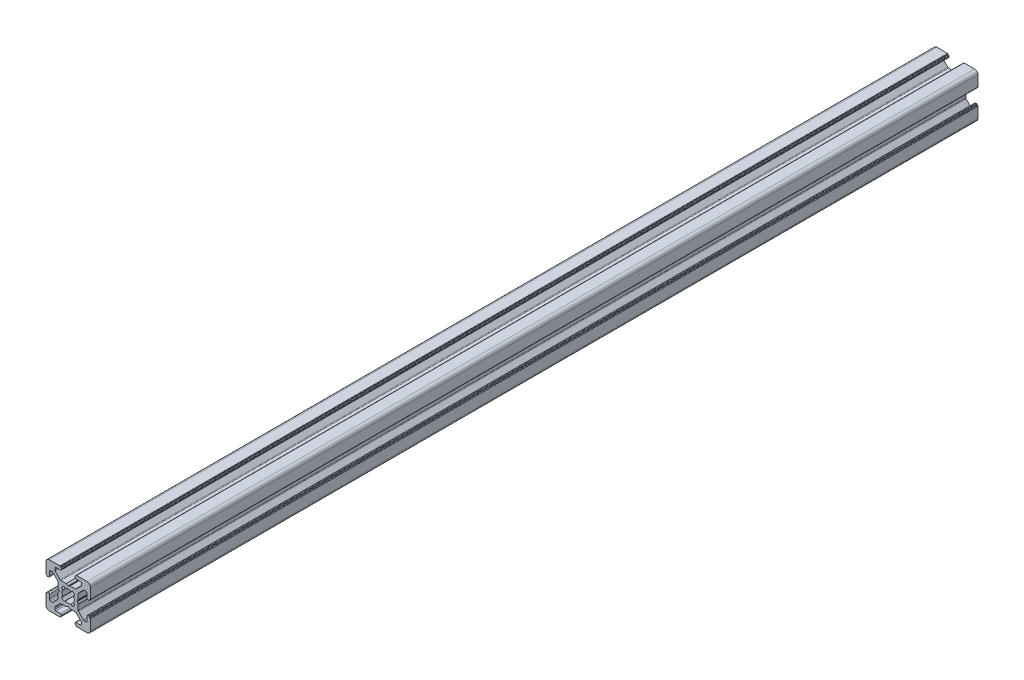
SolidWorks part; units mm, degrees
ref_plane "Płaszczyzna przednia" through (0, 0, 0) normal (0, 0, 1) x (1, 0, 0)
ref_plane "Płaszczyzna górna" through (0, 0, 0) normal (0, 1, 0) x (1, 0, 0)
ref_plane "Płaszczyzna prawa" through (0, 0, 0) normal (1, 0, 0) x (0, 0, -1)
sketch "Szkic1" plane through (0, 0, 0) normal (0, 0, 1) x (1, 0, 0)
  line L0 (7.0078, -1.8401) -> (7.5547, -2.4918)
  line L1 (7.5547, -5.0082) -> (7.0078, -5.6599)
  line L2 (8.0861, -6.7396) -> (8.7418, -6.1953)
  line L3 (11.2582, -6.1953) -> (11.9139, -6.7396)
  line L4 (12.9922, -5.6599) -> (12.4453, -5.0082)
  line L5 (12.4453, -2.4918) -> (12.9922, -1.8401)
  line L6 (11.9139, -0.7604) -> (11.2582, -1.3047)
  line L7 (8.7418, -1.3047) -> (8.0861, -0.7604)
  line L8 (6.25, 6.25) -> (1.5, 6.25)
  line L9 (6.45, 5.95) -> (6.45, 6.05)
  line L10 (6.8, 5.75) -> (6.65, 5.75)
  line L11 (7, 5.25) -> (7, 5.55)
  line L12 (4.5, 4.75) -> (6.5, 4.75)
  line L13 (4, 3.5178) -> (4, 4.25)
  line L14 (6.4142, 0.8964) -> (4.1464, 3.1642)
  line L15 (9.0464, 0.75) -> (6.7678, 0.75)
  line L16 (9.9, 0.2881) -> (9.1464, 0.7232)
  line L17 (10.8536, 0.7232) -> (10.1, 0.2881)
  line L18 (13.2322, 0.75) -> (10.9536, 0.75)
  line L19 (15.8536, 3.1642) -> (13.5858, 0.8964)
  line L20 (16, 4.25) -> (16, 3.5178)
  line L21 (13.5, 4.75) -> (15.5, 4.75)
  line L22 (13, 5.55) -> (13, 5.25)
  line L23 (13.35, 5.75) -> (13.2, 5.75)
  line L24 (13.55, 6.05) -> (13.55, 5.95)
  line L25 (18.5, 6.25) -> (13.75, 6.25)
  line L26 (20, 0) -> (20, 4.75)
  line L27 (19.7, -0.2) -> (19.8, -0.2)
  line L28 (19.5, -0.55) -> (19.5, -0.4)
  line L29 (19, -0.75) -> (19.3, -0.75)
  line L30 (18.5, 1.75) -> (18.5, -0.25)
  line L31 (17.2678, 2.25) -> (18, 2.25)
  line L32 (14.6464, -0.1642) -> (16.9142, 2.1036)
  line L33 (14.5, -2.7964) -> (14.5, -0.5178)
  line L34 (14.0381, -3.65) -> (14.4732, -2.8964)
  line L35 (14.4732, -4.6036) -> (14.0381, -3.85)
  line L36 (14.5, -6.9822) -> (14.5, -4.7036)
  line L37 (16.9142, -9.6036) -> (14.6464, -7.3358)
  line L38 (18, -9.75) -> (17.2678, -9.75)
  line L39 (18.5, -7.25) -> (18.5, -9.25)
  line L40 (19.3, -6.75) -> (19, -6.75)
  line L41 (19.5, -7.1) -> (19.5, -6.95)
  line L42 (19.8, -7.3) -> (19.7, -7.3)
  line L43 (20, -12.25) -> (20, -7.5)
  line L44 (13.75, -13.75) -> (18.5, -13.75)
  line L45 (13.55, -13.45) -> (13.55, -13.55)
  line L46 (13.2, -13.25) -> (13.35, -13.25)
  line L47 (13, -12.75) -> (13, -13.05)
  line L48 (15.5, -12.25) -> (13.5, -12.25)
  line L49 (16, -11.0178) -> (16, -11.75)
  line L50 (13.5858, -8.3964) -> (15.8536, -10.6642)
  line L51 (10.9536, -8.25) -> (13.2322, -8.25)
  line L52 (10.1, -7.7881) -> (10.8536, -8.2232)
  line L53 (9.1464, -8.2232) -> (9.9, -7.7881)
  line L54 (6.7678, -8.25) -> (9.0464, -8.25)
  line L55 (4.1464, -10.6642) -> (6.4142, -8.3964)
  line L56 (4, -11.75) -> (4, -11.0178)
  line L57 (6.5, -12.25) -> (4.5, -12.25)
  line L58 (7, -13.05) -> (7, -12.75)
  line L59 (6.65, -13.25) -> (6.8, -13.25)
  line L60 (6.45, -13.55) -> (6.45, -13.45)
  line L61 (1.5, -13.75) -> (6.25, -13.75)
  line L62 (0, -7.5) -> (0, -12.25)
  line L63 (0.3, -7.3) -> (0.2, -7.3)
  line L64 (0.5, -6.95) -> (0.5, -7.1)
  line L65 (1, -6.75) -> (0.7, -6.75)
  line L66 (1.5, -9.25) -> (1.5, -7.25)
  line L67 (2.7322, -9.75) -> (2, -9.75)
  line L68 (5.3536, -7.3358) -> (3.0858, -9.6036)
  line L69 (5.5, -4.7036) -> (5.5, -6.9822)
  line L70 (5.9619, -3.85) -> (5.5268, -4.6036)
  line L71 (5.5268, -2.8964) -> (5.9619, -3.65)
  line L72 (5.5, -0.5178) -> (5.5, -2.7964)
  line L73 (3.0858, 2.1036) -> (5.3536, -0.1642)
  line L74 (2, 2.25) -> (2.7322, 2.25)
  line L75 (1.5, -0.25) -> (1.5, 1.75)
  line L76 (0.7, -0.75) -> (1, -0.75)
  line L77 (0.5, -0.4) -> (0.5, -0.55)
  line L78 (0.2, -0.2) -> (0.3, -0.2)
  line L79 (0, 4.75) -> (0, 0)
  arc A0 (7.5547, -2.4918) -> (7.5547, -5.0082) centre (10, -3.75) ccw
  arc A1 (7.0078, -5.6599) -> (8.0861, -6.7396) centre (10, -3.75) ccw
  arc A2 (8.7418, -6.1953) -> (11.2582, -6.1953) centre (10, -3.75) ccw
  arc A3 (11.9139, -6.7396) -> (12.9922, -5.6599) centre (10, -3.75) ccw
  arc A4 (12.4453, -5.0082) -> (12.4453, -2.4918) centre (10, -3.75) ccw
  arc A5 (12.9922, -1.8401) -> (11.9139, -0.7604) centre (10, -3.75) ccw
  arc A6 (11.2582, -1.3047) -> (8.7418, -1.3047) centre (10, -3.75) ccw
  arc A7 (8.0861, -0.7604) -> (7.0078, -1.8401) centre (10, -3.75) ccw
  arc A8 (6.45, 6.05) -> (6.25, 6.25) centre (6.25, 6.05) ccw
  arc A9 (6.45, 5.95) -> (6.65, 5.75) centre (6.65, 5.95) ccw
  arc A10 (7, 5.55) -> (6.8, 5.75) centre (6.8, 5.55) ccw
  arc A11 (6.5, 4.75) -> (7, 5.25) centre (6.5, 5.25) ccw
  arc A12 (4.5, 4.75) -> (4, 4.25) centre (4.5, 4.25) ccw
  arc A13 (4, 3.5178) -> (4.1464, 3.1642) centre (4.5, 3.5178) ccw
  arc A14 (6.4142, 0.8964) -> (6.7678, 0.75) centre (6.7678, 1.25) ccw
  arc A15 (9.1464, 0.7232) -> (9.0464, 0.75) centre (9.0464, 0.55) ccw
  arc A16 (9.9, 0.2881) -> (10.1, 0.2881) centre (10, 0.4613) ccw
  arc A17 (10.9536, 0.75) -> (10.8536, 0.7232) centre (10.9536, 0.55) ccw
  arc A18 (13.2322, 0.75) -> (13.5858, 0.8964) centre (13.2322, 1.25) ccw
  arc A19 (15.8536, 3.1642) -> (16, 3.5178) centre (15.5, 3.5178) ccw
  arc A20 (16, 4.25) -> (15.5, 4.75) centre (15.5, 4.25) ccw
  arc A21 (13, 5.25) -> (13.5, 4.75) centre (13.5, 5.25) ccw
  arc A22 (13.2, 5.75) -> (13, 5.55) centre (13.2, 5.55) ccw
  arc A23 (13.35, 5.75) -> (13.55, 5.95) centre (13.35, 5.95) ccw
  arc A24 (13.75, 6.25) -> (13.55, 6.05) centre (13.75, 6.05) ccw
  arc A25 (20, 4.75) -> (18.5, 6.25) centre (18.5, 4.75) ccw
  arc A26 (19.8, -0.2) -> (20, 0) centre (19.8, 0) ccw
  arc A27 (19.7, -0.2) -> (19.5, -0.4) centre (19.7, -0.4) ccw
  arc A28 (19.3, -0.75) -> (19.5, -0.55) centre (19.3, -0.55) ccw
  arc A29 (18.5, -0.25) -> (19, -0.75) centre (19, -0.25) ccw
  arc A30 (18.5, 1.75) -> (18, 2.25) centre (18, 1.75) ccw
  arc A31 (17.2678, 2.25) -> (16.9142, 2.1036) centre (17.2678, 1.75) ccw
  arc A32 (14.6464, -0.1642) -> (14.5, -0.5178) centre (15, -0.5178) ccw
  arc A33 (14.4732, -2.8964) -> (14.5, -2.7964) centre (14.3, -2.7964) ccw
  arc A34 (14.0381, -3.65) -> (14.0381, -3.85) centre (14.2113, -3.75) ccw
  arc A35 (14.5, -4.7036) -> (14.4732, -4.6036) centre (14.3, -4.7036) ccw
  arc A36 (14.5, -6.9822) -> (14.6464, -7.3358) centre (15, -6.9822) ccw
  arc A37 (16.9142, -9.6036) -> (17.2678, -9.75) centre (17.2678, -9.25) ccw
  arc A38 (18, -9.75) -> (18.5, -9.25) centre (18, -9.25) ccw
  arc A39 (19, -6.75) -> (18.5, -7.25) centre (19, -7.25) ccw
  arc A40 (19.5, -6.95) -> (19.3, -6.75) centre (19.3, -6.95) ccw
  arc A41 (19.5, -7.1) -> (19.7, -7.3) centre (19.7, -7.1) ccw
  arc A42 (20, -7.5) -> (19.8, -7.3) centre (19.8, -7.5) ccw
  arc A43 (18.5, -13.75) -> (20, -12.25) centre (18.5, -12.25) ccw
  arc A44 (13.55, -13.55) -> (13.75, -13.75) centre (13.75, -13.55) ccw
  arc A45 (13.55, -13.45) -> (13.35, -13.25) centre (13.35, -13.45) ccw
  arc A46 (13, -13.05) -> (13.2, -13.25) centre (13.2, -13.05) ccw
  arc A47 (13.5, -12.25) -> (13, -12.75) centre (13.5, -12.75) ccw
  arc A48 (15.5, -12.25) -> (16, -11.75) centre (15.5, -11.75) ccw
  arc A49 (16, -11.0178) -> (15.8536, -10.6642) centre (15.5, -11.0178) ccw
  arc A50 (13.5858, -8.3964) -> (13.2322, -8.25) centre (13.2322, -8.75) ccw
  arc A51 (10.8536, -8.2232) -> (10.9536, -8.25) centre (10.9536, -8.05) ccw
  arc A52 (10.1, -7.7881) -> (9.9, -7.7881) centre (10, -7.9613) ccw
  arc A53 (9.0464, -8.25) -> (9.1464, -8.2232) centre (9.0464, -8.05) ccw
  arc A54 (6.7678, -8.25) -> (6.4142, -8.3964) centre (6.7678, -8.75) ccw
  arc A55 (4.1464, -10.6642) -> (4, -11.0178) centre (4.5, -11.0178) ccw
  arc A56 (4, -11.75) -> (4.5, -12.25) centre (4.5, -11.75) ccw
  arc A57 (7, -12.75) -> (6.5, -12.25) centre (6.5, -12.75) ccw
  arc A58 (6.8, -13.25) -> (7, -13.05) centre (6.8, -13.05) ccw
  arc A59 (6.65, -13.25) -> (6.45, -13.45) centre (6.65, -13.45) ccw
  arc A60 (6.25, -13.75) -> (6.45, -13.55) centre (6.25, -13.55) ccw
  arc A61 (0, -12.25) -> (1.5, -13.75) centre (1.5, -12.25) ccw
  arc A62 (0.2, -7.3) -> (0, -7.5) centre (0.2, -7.5) ccw
  arc A63 (0.3, -7.3) -> (0.5, -7.1) centre (0.3, -7.1) ccw
  arc A64 (0.7, -6.75) -> (0.5, -6.95) centre (0.7, -6.95) ccw
  arc A65 (1.5, -7.25) -> (1, -6.75) centre (1, -7.25) ccw
  arc A66 (1.5, -9.25) -> (2, -9.75) centre (2, -9.25) ccw
  arc A67 (2.7322, -9.75) -> (3.0858, -9.6036) centre (2.7322, -9.25) ccw
  arc A68 (5.3536, -7.3358) -> (5.5, -6.9822) centre (5, -6.9822) ccw
  arc A69 (5.5268, -4.6036) -> (5.5, -4.7036) centre (5.7, -4.7036) ccw
  arc A70 (5.9619, -3.85) -> (5.9619, -3.65) centre (5.7887, -3.75) ccw
  arc A71 (5.5, -2.7964) -> (5.5268, -2.8964) centre (5.7, -2.7964) ccw
  arc A72 (5.5, -0.5178) -> (5.3536, -0.1642) centre (5, -0.5178) ccw
  arc A73 (3.0858, 2.1036) -> (2.7322, 2.25) centre (2.7322, 1.75) ccw
  arc A74 (2, 2.25) -> (1.5, 1.75) centre (2, 1.75) ccw
  arc A75 (1, -0.75) -> (1.5, -0.25) centre (1, -0.25) ccw
  arc A76 (0.5, -0.55) -> (0.7, -0.75) centre (0.7, -0.55) ccw
  arc A77 (0.5, -0.4) -> (0.3, -0.2) centre (0.3, -0.4) ccw
  arc A78 (0, 0) -> (0.2, -0.2) centre (0.2, 0) ccw
  arc A79 (1.5, 6.25) -> (0, 4.75) centre (1.5, 4.75) ccw
  dimension "D4" = 2.75
  dimension "D1" = 20
  dimension "D2" = 20
  dimension "D3" = 6
extrude "Dodanie-wyciągnięcie1" add sketch "Szkic1" along normal blind 400
